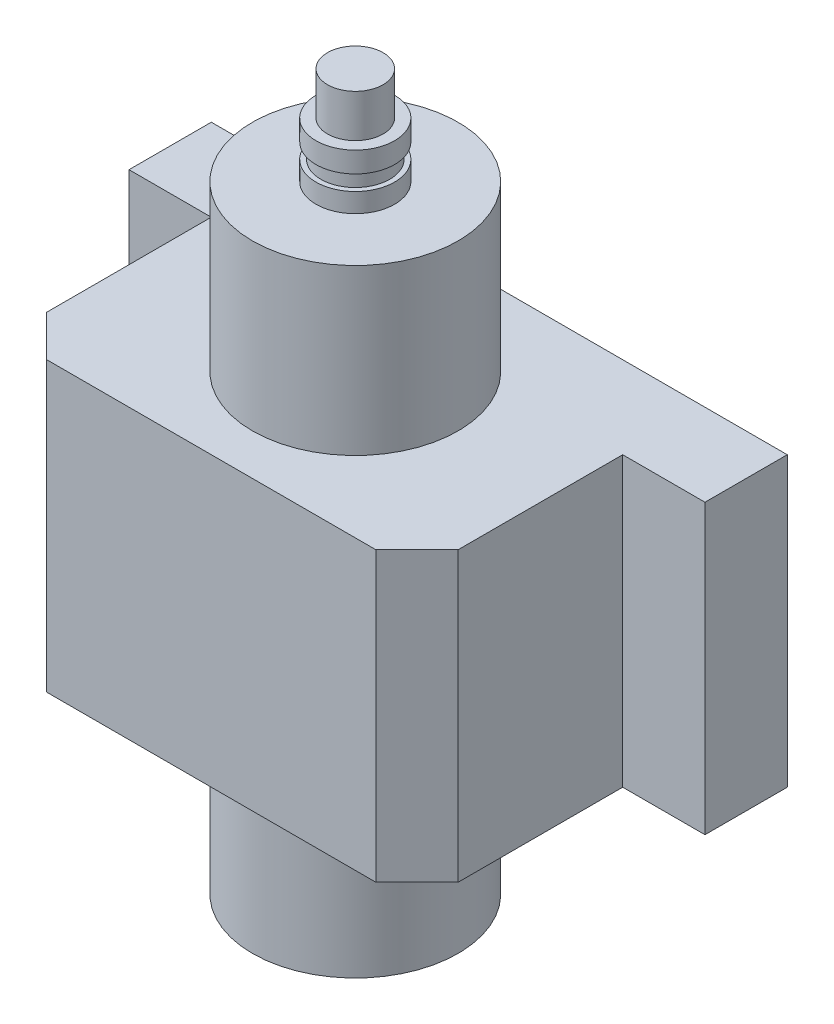
SolidWorks part; units mm, degrees
ref_plane "Front Plane" through (0, 0, 0) normal (0, 0, 1) x (1, 0, 0)
ref_plane "Top Plane" through (0, 0, 0) normal (0, 1, 0) x (1, 0, 0)
ref_plane "Right Plane" through (0, 0, 0) normal (1, 0, 0) x (0, 0, -1)
sketch "Sketch1" plane through (0, 0, 0) normal (0, 1, 0) x (1, 0, 0)
  line L0 (70, 0) -> (-70, 0)
  line L1 (-70, 0) -> (-70, -20)
  line L2 (-70, -20) -> (-50, -20)
  line L3 (-50, -20) -> (-50, -70)
  line L4 (-50, -70) -> (50, -70)
  line L5 (0, -70) -> (0, 0) construction
  line L6 (50, -20) -> (50, -70)
  line L7 (70, -20) -> (50, -20)
  line L8 (70, 0) -> (70, -20)
  circle A0 centre (0, -35) radius 25
  dimension "D5" = 50
  dimension "D1" = 20
  dimension "D2" = 50
  dimension "D3" = 100
  dimension "D4" = 70
extrude "Boss-Extrude1" add sketch "Sketch1" along normal blind 70
ref_plane "Plane1" through (0, 35, 0) normal (0, 1, 0) x (1, 0, 0)
sketch "Sketch3" plane through (0, 35, 0) normal (0, 1, 0) x (1, 0, 0)
  circle A0 centre (0, -35) radius 25 construction
  circle A1 centre (0, -35) radius 25
extrude "Boss-Extrude2" add sketch "Sketch3" along normal mid plane 150
ref_plane "Plane2" through (0, 0, 60) normal (0, 0, 1) x (1, 0, 0)
ref_plane "Plane3" through (0, 0, 35) normal (0, 0, 1) x (1, 0, 0)
sketch "Sketch4" plane through (0, 0, 35) normal (0, 0, 1) x (1, 0, 0)
  line L0 (-25, -40) -> (25, -40) construction
  line L1 (-25, -40) -> (25, -40)
  line L2 (25, 110) -> (-25, 110) construction
  line L3 (25, 110) -> (-25, 110)
  line L4 (0, -40) -> (0, -77.5611)
  line L5 (-9.564, -40) -> (-9.564, -50.7006)
  line L6 (-9.564, -50.7006) -> (-4.8915, -50.7006)
  line L7 (-4.8915, -50.7006) -> (-4.8915, -52.4179)
  line L8 (-4.8915, -52.4179) -> (0, -52.4179)
  line L9 (0, 110) -> (0, 146.8004)
  line L10 (-9.564, 110) -> (-9.564, 114.6686)
  line L11 (-9.564, 114.6686) -> (-8.3895, 114.6686)
  line L12 (-8.3895, 114.6686) -> (-8.3895, 118.3574)
  line L13 (-8.3895, 118.3574) -> (-9.564, 118.3574)
  line L14 (-9.564, 118.3574) -> (-9.564, 123.3836)
  line L15 (-9.564, 123.3836) -> (-6.7548, 123.3836)
  line L16 (-6.7548, 123.3836) -> (-6.7548, 133.7661)
  line L17 (-6.7548, 133.7661) -> (0, 133.7661)
  point P23 (-4.8915, 118.3574)
revolve "Revolve1" add sketch "Sketch4" angle 360 about L4
chamfer "Chamfer1" distance 10 angle 45 2 edges at (50, 35, 70) (-50, 35, 70)
